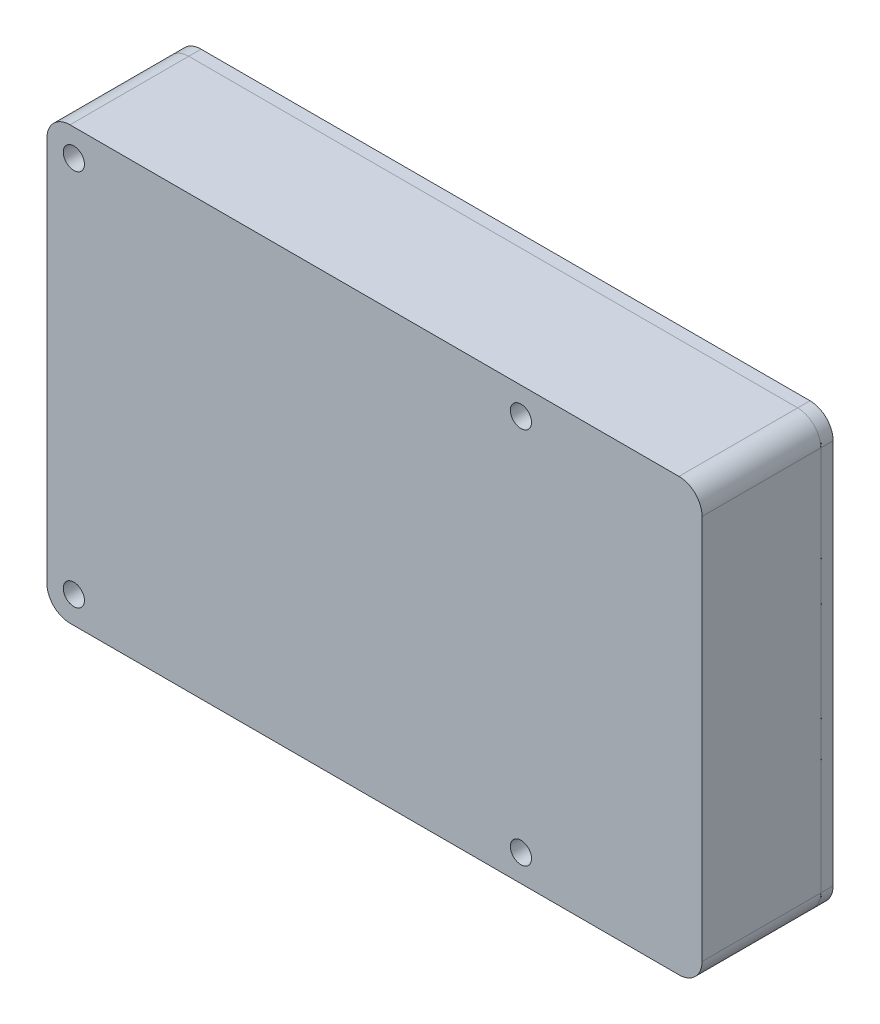
SolidWorks part; units mm, degrees
ref_plane "Front Plane" through (0, 0, 0) normal (0, 0, 1) x (1, 0, 0)
ref_plane "Top Plane" through (0, 0, 0) normal (0, 1, 0) x (1, 0, 0)
ref_plane "Right Plane" through (0, 0, 0) normal (1, 0, 0) x (0, 0, -1)
sketch "Sketch1" plane through (0, 0, 0) normal (0, 0, 1) x (1, 0, 0)
  line L1 (-39.5, -28) -> (39.5, -28)
  line L2 (-42.5, -25) -> (-42.5, 25)
  line L3 (-39.5, 28) -> (39.5, 28)
  line L4 (42.5, -25) -> (42.5, 25)
  line L5 (-42.5, -28) -> (42.5, 28) construction
  line L6 (-42.5, 28) -> (42.5, -28) construction
  arc A0 (-39.5, -28) -> (-42.5, -25) centre (-39.5, -25) cw
  arc A1 (39.5, -28) -> (42.5, -25) centre (39.5, -25) ccw
  arc A2 (39.5, 28) -> (42.5, 25) centre (39.5, 25) cw
  arc A3 (-42.5, 25) -> (-39.5, 28) centre (-39.5, 25) cw
  circle A4 centre (-39, 24.5) radius 1.375
  circle A5 centre (-39, -24.5) radius 1.375
  circle A6 centre (19, 24.5) radius 1.375
  circle A7 centre (19, -24.5) radius 1.375
  point P0 (0, 0)
  dimension "D3" = 3
  dimension "D4" = 2.75
  dimension "D5" = 3.5
  dimension "D6" = 3.5
  dimension "D7" = 58
  dimension "D8" = 58
  dimension "D9" = 49
  dimension "D12" = 49
  dimension "D1" = 85
  dimension "D2" = 56
  dimension "D10" = 24.5
  dimension "D11" = 24.5
extrude "Boss-Extrude1" add sketch "Sketch1" along normal blind 1.6
sketch "Sketch2" plane through (0, 0, 1.6) normal (0, 0, 1) x (1, 0, 0)
  line L1 (-42.5, 25) -> (-42.5, -25) construction
  line L2 (-35.65, -28.6369) -> (-28.15, -28.6369)
  line L3 (-35.65, -28.6369) -> (-35.65, -23.2)
  line L4 (-35.65, -23.2) -> (-32.465, -23.2)
  line L5 (-28.15, -28.6369) -> (-28.15, -23.2)
  line L6 (-35.65, -28.6369) -> (-28.15, -23.2) construction
  line L7 (-35.65, -23.2) -> (-28.15, -28.6369) construction
  line L8 (-39.5, -28) -> (39.5, -28) construction
  line L9 (-17.75, -17.5) -> (-11.0158, -17.5)
  line L10 (-17.75, -17.5) -> (-17.75, -33.1614)
  line L11 (-17.75, -33.1614) -> (-3.25, -33.1614)
  line L12 (-3.25, -17.5) -> (-3.25, -33.1614)
  line L13 (-17.75, -17.5) -> (-3.25, -33.1614) construction
  line L14 (-17.75, -33.1614) -> (-3.25, -17.5) construction
  line L15 (0.5, -5.3) -> (4.5, -5.3)
  line L16 (0.5, -5.3) -> (0.5, -15.174)
  line L17 (0.5, -27.7) -> (4.5, -27.7)
  line L18 (4.5, -5.3) -> (4.5, -27.7)
  line L19 (0.5, -5.3) -> (4.5, -27.7) construction
  line L20 (0.5, -27.7) -> (4.5, -5.3) construction
  line L21 (7.5, -15.5) -> (9.7992, -15.5)
  line L22 (7.5, -15.5) -> (7.5, -31.1614)
  line L23 (7.5, -31.1614) -> (14.5, -31.1614)
  line L24 (14.5, -15.5) -> (14.5, -31.1614)
  line L25 (7.5, -15.5) -> (14.5, -31.1614) construction
  line L26 (7.5, -31.1614) -> (14.5, -15.5) construction
  line L27 (-35.45, 27) -> (15.45, 27)
  line L28 (-35.45, 27) -> (-35.45, 22)
  line L29 (-35.45, 22) -> (-11.4582, 22)
  line L30 (15.45, 27) -> (15.45, 22)
  line L31 (-35.45, 27) -> (15.45, 22) construction
  line L32 (-35.45, 22) -> (15.45, 27) construction
  line L33 (-41.3717, -10.5142) -> (-37.3717, -10.5142)
  line L34 (-41.3717, -10.5142) -> (-41.3717, 10.5142)
  line L35 (-41.3717, 10.5142) -> (-37.3717, 10.5142)
  line L36 (-37.3717, -10.5142) -> (-37.3717, 0.0947)
  line L37 (-41.3717, -10.5142) -> (-37.3717, 10.5142) construction
  line L38 (-41.3717, 10.5142) -> (-37.3717, -10.5142) construction
  line L39 (42.5, -25) -> (42.5, 25) construction
  line L40 (23.2, -25.5) -> (44.7, -25.5)
  line L41 (23.2, -25.5) -> (23.2, -17.75)
  line L42 (23.2, -10) -> (44.7, -10)
  line L43 (44.7, -25.5) -> (44.7, -10)
  line L44 (23.2, -25.5) -> (44.7, -10) construction
  line L45 (23.2, -10) -> (44.7, -25.5) construction
  line L46 (26.8, -5.5) -> (54.0714, -5.5)
  line L47 (26.8, -5.5) -> (26.8, 0.4072)
  line L48 (26.8, 7.5) -> (54.0714, 7.5)
  line L49 (54.0714, -5.5) -> (54.0714, 7.5)
  line L50 (26.8, -5.5) -> (54.0714, 7.5) construction
  line L51 (26.8, 7.5) -> (54.0714, -5.5) construction
  line L52 (26.8, 12.5) -> (57.7137, 12.5)
  line L53 (26.8, 12.5) -> (26.8, 18.6113)
  line L54 (26.8, 25.5) -> (57.7137, 25.5)
  line L55 (57.7137, 12.5) -> (57.7137, 25.5)
  line L56 (26.8, 12.5) -> (57.7137, 25.5) construction
  line L57 (26.8, 25.5) -> (57.7137, 12.5) construction
  line L58 (-35.35, 22.1) -> (-11.4582, 22.1)
  line L59 (15.35, 26.9) -> (15.35, 22.1)
  line L60 (-35.35, 26.9) -> (15.35, 26.9)
  line L61 (-35.35, 26.9) -> (-35.35, 22.1)
  line L62 (-41.2717, 10.4142) -> (-37.4717, 10.4142)
  line L63 (-37.4717, -10.4142) -> (-37.4717, 0.0947)
  line L64 (-41.2717, -10.4142) -> (-37.4717, -10.4142)
  line L65 (-41.2717, -10.4142) -> (-41.2717, 10.4142)
  line L66 (-35.55, -28.5369) -> (-35.55, -23.3)
  line L67 (-35.55, -23.3) -> (-32.465, -23.3)
  line L68 (-28.25, -28.5369) -> (-28.25, -23.3)
  line L69 (-35.55, -28.5369) -> (-28.25, -28.5369)
  line L70 (-17.65, -17.6) -> (-17.65, -33.0614)
  line L71 (-17.65, -33.0614) -> (-3.35, -33.0614)
  line L72 (-3.35, -17.6) -> (-3.35, -33.0614)
  line L73 (-17.65, -17.6) -> (-11.0158, -17.6)
  line L74 (0.6, -5.4) -> (0.6, -15.174)
  line L75 (0.6, -27.6) -> (4.4, -27.6)
  line L76 (4.4, -5.4) -> (4.4, -27.6)
  line L77 (0.6, -5.4) -> (4.4, -5.4)
  line L78 (7.6, -15.6) -> (9.7992, -15.6)
  line L79 (14.4, -15.6) -> (14.4, -31.0614)
  line L80 (7.6, -31.0614) -> (14.4, -31.0614)
  line L81 (7.6, -15.6) -> (7.6, -31.0614)
  line L82 (23.3, -25.4) -> (23.3, -17.75)
  line L83 (23.3, -10.1) -> (44.6, -10.1)
  line L84 (44.6, -25.4) -> (44.6, -10.1)
  line L85 (23.3, -25.4) -> (44.6, -25.4)
  line L86 (26.9, -5.4) -> (53.9714, -5.4)
  line L87 (53.9714, -5.4) -> (53.9714, 7.4)
  line L88 (26.9, 7.4) -> (53.9714, 7.4)
  line L89 (26.9, -5.4) -> (26.9, 0.4072)
  line L90 (26.9, 12.6) -> (57.6137, 12.6)
  line L91 (57.6137, 12.6) -> (57.6137, 25.4)
  line L92 (26.9, 25.4) -> (57.6137, 25.4)
  line L93 (26.9, 12.6) -> (26.9, 18.6113)
  line L94 (-37.4717, 1) -> (-37.4717, 10.4142)
  line L95 (-37.4717, 1) -> (-37.3717, 1)
  line L96 (26.9, 20.2773) -> (26.9, 25.4)
  line L97 (-37.4717, 0.0947) -> (-37.3717, 0.0947)
  line L98 (26.9, 12.6) -> (26.9, 25.4) construction
  line L99 (-37.4717, -10.4142) -> (-37.4717, 10.4142) construction
  line L100 (-37.3717, 1) -> (-37.3717, 10.5142)
  line L101 (-37.3717, -10.5142) -> (-37.3717, 10.5142) construction
  line L102 (26.8, 20.2773) -> (26.9, 20.2773)
  line L103 (26.9, 2.5528) -> (26.9, 7.4)
  line L104 (26.8, 18.6113) -> (26.9, 18.6113)
  line L105 (26.9, -5.4) -> (26.9, 7.4) construction
  line L106 (26.8, 20.2773) -> (26.8, 25.5)
  line L107 (26.8, 12.5) -> (26.8, 25.5) construction
  line L108 (23.2, -16.5) -> (23.3, -16.5)
  line L109 (12.0626, -15.5) -> (14.5, -15.5)
  line L110 (23.2, -17.75) -> (23.3, -17.75)
  line L111 (7.5, -15.5) -> (14.5, -15.5) construction
  line L112 (26.8, 2.5528) -> (26.9, 2.5528)
  line L113 (23.2, -16.5) -> (23.2, -10)
  line L114 (26.8, 0.4072) -> (26.9, 0.4072)
  line L115 (23.2, -25.5) -> (23.2, -10) construction
  line L116 (-8.9067, 22.1) -> (15.35, 22.1)
  line L117 (-32.465, -23.2) -> (-32.465, -23.3)
  line L118 (-35.35, 22.1) -> (15.35, 22.1) construction
  line L119 (-31.5737, -23.2) -> (-31.5737, -23.3)
  line L120 (-31.5737, -23.3) -> (-28.25, -23.3)
  line L121 (-11.0158, -17.5) -> (-11.0158, -17.6)
  line L122 (-35.55, -23.3) -> (-28.25, -23.3) construction
  line L123 (-9.6849, -17.5) -> (-9.6849, -17.6)
  line L124 (0.5, -15.174) -> (0.6, -15.174)
  line L125 (-9.6849, -17.5) -> (-3.25, -17.5)
  line L126 (0.5, -17.125) -> (0.6, -17.125)
  line L127 (-17.75, -17.5) -> (-3.25, -17.5) construction
  line L128 (0.5, -17.125) -> (0.5, -27.7)
  line L129 (9.7992, -15.5) -> (9.7992, -15.6)
  line L130 (0.5, -5.3) -> (0.5, -27.7) construction
  line L131 (12.0626, -15.5) -> (12.0626, -15.6)
  line L132 (26.8, 2.5528) -> (26.8, 7.5)
  line L133 (26.8, -5.5) -> (26.8, 7.5) construction
  line L134 (23.3, -16.5) -> (23.3, -10.1)
  line L135 (23.3, -25.4) -> (23.3, -10.1) construction
  line L136 (12.0626, -15.6) -> (14.4, -15.6)
  line L137 (7.6, -15.6) -> (14.4, -15.6) construction
  line L138 (0.6, -17.125) -> (0.6, -27.6)
  line L139 (0.6, -5.4) -> (0.6, -27.6) construction
  line L140 (-9.6849, -17.6) -> (-3.35, -17.6)
  line L141 (-17.65, -17.6) -> (-3.35, -17.6) construction
  line L142 (-31.5737, -23.2) -> (-28.15, -23.2)
  line L143 (-35.65, -23.2) -> (-28.15, -23.2) construction
  line L145 (-11.4582, 22.1) -> (-11.4582, 22)
  line L147 (-8.9067, 22.1) -> (-8.9067, 22)
  line L148 (-8.9067, 22) -> (15.45, 22)
  line L149 (-35.45, 22) -> (15.45, 22) construction
  circle A0 centre (-39, 24.5) radius 1.375 construction
  point P0 (-31.9, -25.9184)
  point P7 (-10.5, -25.3307)
  point P12 (2.5, -16.5)
  point P17 (11, -23.3307)
  point P22 (-10, 24.5)
  point P29 (-39.3717, 0)
  point P36 (33.95, -17.75)
  point P41 (40.4357, 1)
  point P46 (42.2569, 19)
  dimension "D5" = 29
  dimension "D26" = 0
  dimension "D1" = 10.6
  dimension "D2" = 32
  dimension "D3" = 13
  dimension "D4" = 53.5
  dimension "D6" = 28
  dimension "D7" = 11.5
  dimension "D8" = 10.25
  dimension "D9" = 29
  dimension "D10" = 47
  dimension "D11" = 7.5
  dimension "D12" = 4.8
  dimension "D13" = 14.5
  dimension "D14" = 10.5
  dimension "D15" = 4
  dimension "D16" = 22.7
  dimension "D17" = 7
  dimension "D18" = 12.5
  dimension "D19" = 15.5
  dimension "D20" = 19.3
  dimension "D21" = 21.5
  dimension "D22" = 13
  dimension "D23" = 13
  dimension "D24" = 15.7
  dimension "D25" = 15.7
  dimension "D27" = 5
  dimension "D28" = 50.9
  dimension "D29" = 4
  dimension "D30" = 0.1
extrude "Cut-Extrude1" cut sketch "Sketch2" against normal blind 0.1
sketch "Эскиз1" plane through (0, 0, 1.6) normal (0, 0, 1) x (1, 0, 0)
  line L1 (42.5, -25) -> (42.5, 25) construction
  line L2 (42.5, -25) -> (42.5, 25)
  line L3 (39.5, 28) -> (-39.5, 28) construction
  line L4 (39.5, 28) -> (-39.5, 28)
  line L5 (-42.5, 25) -> (-42.5, -25) construction
  line L6 (-42.5, 25) -> (-42.5, -25)
  line L7 (-39.5, -28) -> (39.5, -28) construction
  line L8 (-39.5, -28) -> (39.5, -28)
  line L9 (42.5, -25) -> (42.5, 25)
  arc A0 (42.5, 25) -> (39.5, 28) centre (39.5, 25) ccw construction
  arc A1 (42.5, 25) -> (39.5, 28) centre (39.5, 25) ccw
  arc A2 (-39.5, 28) -> (-42.5, 25) centre (-39.5, 25) ccw construction
  arc A3 (-39.5, 28) -> (-42.5, 25) centre (-39.5, 25) ccw
  arc A4 (-42.5, -25) -> (-39.5, -28) centre (-39.5, -25) ccw construction
  arc A5 (-42.5, -25) -> (-39.5, -28) centre (-39.5, -25) ccw
  arc A6 (39.5, -28) -> (42.5, -25) centre (39.5, -25) ccw construction
  arc A7 (39.5, -28) -> (42.5, -25) centre (39.5, -25) ccw
  circle A8 centre (19, 24.5) radius 1.375 construction
  circle A9 centre (-39, 24.5) radius 1.375 construction
  circle A10 centre (-39, -24.5) radius 1.375 construction
  circle A11 centre (19, -24.5) radius 1.375 construction
  circle A12 centre (19, 24.5) radius 1.375
  circle A13 centre (-39, 24.5) radius 1.375
  circle A14 centre (-39, -24.5) radius 1.375
  circle A15 centre (19, -24.5) radius 1.375
extrude "Бобышка-Вытянуть1" add sketch "Эскиз1" along normal blind 15.4 separate body contours L8 A7 L2 A1 L4 A3 L6 A5 A15 A14 A13 A12
